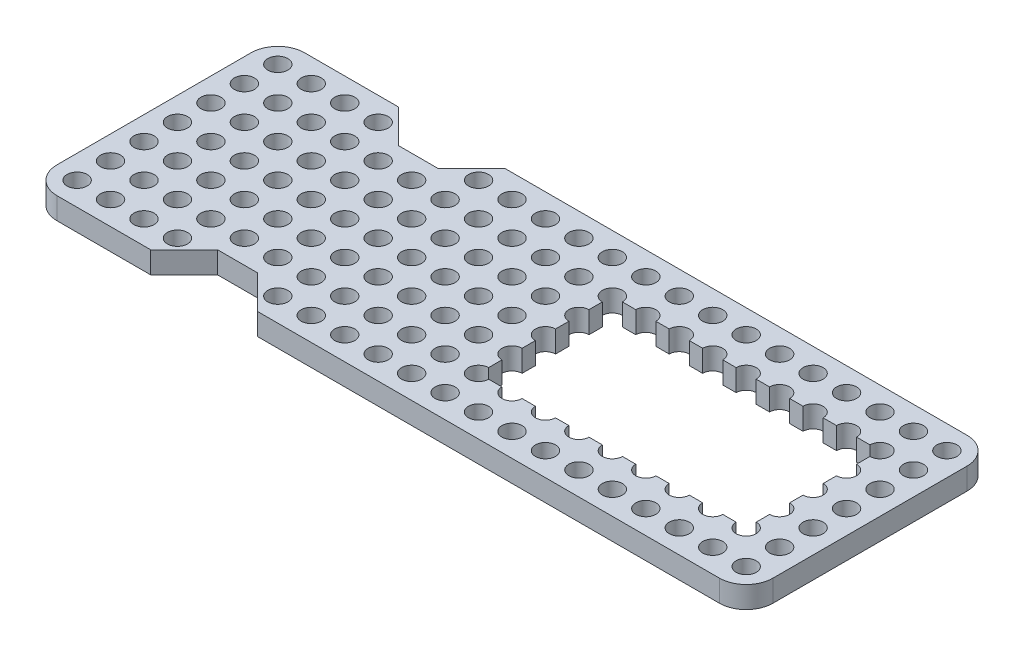
SolidWorks part; units mm, degrees
material "ABS"
ref_plane "Front Plane" through (0, 0, 0) normal (0, 0, 1) x (1, 0, 0)
ref_plane "Top Plane" through (0, 0, 0) normal (0, 1, 0) x (1, 0, 0)
ref_plane "Right Plane" through (0, 0, 0) normal (1, 0, 0) x (0, 0, -1)
sketch "Sketch1" plane through (0, 0, 0) normal (0, 1, 0) x (1, 0, 0)
  line L0 (-35.5, 18.5) -> (-35.5, -18.5) construction
  line L1 (-49.5, 18.5) -> (-35.5, 18.5)
  line L2 (-53.5, 14.5) -> (-53.5, -14.5)
  line L3 (-49.5, -18.5) -> (-35.5, -18.5)
  line L4 (53.5, 14.5) -> (53.5, -14.5)
  line L5 (-53.5, 18.5) -> (53.5, -18.5) construction
  line L6 (-19.5, -18.5) -> (-24.5, -13.5)
  line L7 (-24.5, -13.5) -> (-30.5, -13.5)
  line L8 (-30.5, -13.5) -> (-35.5, -18.5)
  line L9 (-35.5, 18.5) -> (-30.5, 13.5)
  line L10 (-30.5, 13.5) -> (-24.5, 13.5)
  line L11 (-24.5, 13.5) -> (-19.5, 18.5)
  line L12 (-19.5, -18.5) -> (49.5, -18.5)
  line L13 (-19.5, 18.5) -> (49.5, 18.5)
  line L14 (45, -10) -> (45, 10)
  line L15 (45, 10) -> (5, 10)
  line L16 (5, 10) -> (5, -10)
  line L17 (5, -10) -> (45, -10)
  arc A0 (-49.5, 18.5) -> (-53.5, 14.5) centre (-49.5, 14.5) ccw
  arc A1 (-53.5, -14.5) -> (-49.5, -18.5) centre (-49.5, -14.5) ccw
  arc A2 (49.5, -18.5) -> (53.5, -14.5) centre (49.5, -14.5) ccw
  arc A3 (49.5, 18.5) -> (53.5, 14.5) centre (49.5, 14.5) cw
  circle A4 centre (-50, -15) radius 1.5025
  circle A5 centre (-45, -15) radius 1.5025
  circle A6 centre (-40, -15) radius 1.5025
  circle A7 centre (-35, -15) radius 1.5025
  circle A10 centre (-20, -15) radius 1.5025
  circle A11 centre (-15, -15) radius 1.5025
  circle A12 centre (-10, -15) radius 1.5025
  circle A13 centre (-5, -15) radius 1.5025
  circle A14 centre (0, -15) radius 1.5025
  circle A15 centre (5, -15) radius 1.5025
  circle A16 centre (10, -15) radius 1.5025
  circle A17 centre (15, -15) radius 1.5025
  circle A18 centre (20, -15) radius 1.5025
  circle A19 centre (25, -15) radius 1.5025
  circle A20 centre (30, -15) radius 1.5025
  circle A21 centre (35, -15) radius 1.5025
  circle A22 centre (40, -15) radius 1.5025
  circle A23 centre (45, -15) radius 1.5025
  circle A24 centre (50, -15) radius 1.5025
  circle A25 centre (-45, -10) radius 1.5025
  circle A26 centre (-40, -10) radius 1.5025
  circle A27 centre (-35, -10) radius 1.5025
  circle A28 centre (-30, -10) radius 1.5025
  circle A29 centre (-25, -10) radius 1.5025
  circle A30 centre (-20, -10) radius 1.5025
  circle A31 centre (-15, -10) radius 1.5025
  circle A32 centre (-10, -10) radius 1.5025
  circle A33 centre (-5, -10) radius 1.5025
  circle A34 centre (0, -10) radius 1.5025
  arc A35 (5, -8.4975) -> (6.5025, -10) centre (5, -10) ccw
  arc A36 (8.4975, -10) -> (11.5025, -10) centre (10, -10) ccw
  arc A37 (13.4975, -10) -> (16.5025, -10) centre (15, -10) ccw
  arc A38 (18.4975, -10) -> (21.5025, -10) centre (20, -10) ccw
  arc A39 (23.4975, -10) -> (26.5025, -10) centre (25, -10) ccw
  arc A40 (28.4975, -10) -> (31.5025, -10) centre (30, -10) ccw
  arc A41 (33.4975, -10) -> (36.5025, -10) centre (35, -10) ccw
  arc A42 (38.4975, -10) -> (41.5025, -10) centre (40, -10) ccw
  arc A43 (43.4975, -10) -> (45, -8.4975) centre (45, -10) ccw
  circle A44 centre (50, -10) radius 1.5025
  circle A45 centre (-45, -5) radius 1.5025
  circle A46 centre (-40, -5) radius 1.5025
  circle A47 centre (-35, -5) radius 1.5025
  circle A48 centre (-30, -5) radius 1.5025
  circle A49 centre (-25, -5) radius 1.5025
  circle A50 centre (-20, -5) radius 1.5025
  circle A51 centre (-15, -5) radius 1.5025
  circle A52 centre (-10, -5) radius 1.5025
  circle A53 centre (-5, -5) radius 1.5025
  circle A54 centre (0, -5) radius 1.5025
  arc A55 (5, -3.4975) -> (5, -6.5025) centre (5, -5) ccw
  arc A63 (45, -6.5025) -> (45, -3.4975) centre (45, -5) ccw
  circle A64 centre (50, -5) radius 1.5025
  circle A65 centre (-45, 0) radius 1.5025
  circle A66 centre (-40, 0) radius 1.5025
  circle A67 centre (-35, 0) radius 1.5025
  circle A68 centre (-30, 0) radius 1.5025
  circle A69 centre (-25, 0) radius 1.5025
  circle A70 centre (-20, 0) radius 1.5025
  circle A71 centre (-15, 0) radius 1.5025
  circle A72 centre (-10, 0) radius 1.5025
  circle A73 centre (-5, 0) radius 1.5025
  circle A74 centre (0, 0) radius 1.5025
  arc A75 (5, 1.5025) -> (5, -1.5025) centre (5, 0) ccw
  arc A83 (45, -1.5025) -> (45, 1.5025) centre (45, 0) ccw
  circle A84 centre (50, 0) radius 1.5025
  circle A85 centre (-45, 5) radius 1.5025
  circle A86 centre (-40, 5) radius 1.5025
  circle A87 centre (-35, 5) radius 1.5025
  circle A88 centre (-30, 5) radius 1.5025
  circle A89 centre (-25, 5) radius 1.5025
  circle A90 centre (-20, 5) radius 1.5025
  circle A91 centre (-15, 5) radius 1.5025
  circle A92 centre (-10, 5) radius 1.5025
  circle A93 centre (-5, 5) radius 1.5025
  circle A94 centre (0, 5) radius 1.5025
  arc A95 (5, 6.5025) -> (5, 3.4975) centre (5, 5) ccw
  arc A103 (45, 3.4975) -> (45, 6.5025) centre (45, 5) ccw
  circle A104 centre (50, 5) radius 1.5025
  circle A105 centre (-45, 10) radius 1.5025
  circle A106 centre (-40, 10) radius 1.5025
  circle A107 centre (-35, 10) radius 1.5025
  circle A108 centre (-30, 10) radius 1.5025
  circle A109 centre (-25, 10) radius 1.5025
  circle A110 centre (-20, 10) radius 1.5025
  circle A111 centre (-15, 10) radius 1.5025
  circle A112 centre (-10, 10) radius 1.5025
  circle A113 centre (-5, 10) radius 1.5025
  circle A114 centre (0, 10) radius 1.5025
  arc A115 (6.5025, 10) -> (5, 8.4975) centre (5, 10) ccw
  arc A116 (11.5025, 10) -> (8.4975, 10) centre (10, 10) ccw
  arc A117 (16.5025, 10) -> (13.4975, 10) centre (15, 10) ccw
  arc A118 (21.5025, 10) -> (18.4975, 10) centre (20, 10) ccw
  arc A119 (26.5025, 10) -> (23.4975, 10) centre (25, 10) ccw
  arc A120 (31.5025, 10) -> (28.4975, 10) centre (30, 10) ccw
  arc A121 (36.5025, 10) -> (33.4975, 10) centre (35, 10) ccw
  arc A122 (41.5025, 10) -> (38.4975, 10) centre (40, 10) ccw
  arc A123 (45, 8.4975) -> (43.4975, 10) centre (45, 10) ccw
  circle A124 centre (50, 10) radius 1.5025
  circle A125 centre (-45, 15) radius 1.5025
  circle A126 centre (-40, 15) radius 1.5025
  circle A127 centre (-35, 15) radius 1.5025
  circle A130 centre (-20, 15) radius 1.5025
  circle A131 centre (-15, 15) radius 1.5025
  circle A132 centre (-10, 15) radius 1.5025
  circle A133 centre (-5, 15) radius 1.5025
  circle A134 centre (0, 15) radius 1.5025
  circle A135 centre (5, 15) radius 1.5025
  circle A136 centre (10, 15) radius 1.5025
  circle A137 centre (15, 15) radius 1.5025
  circle A138 centre (20, 15) radius 1.5025
  circle A139 centre (25, 15) radius 1.5025
  circle A140 centre (30, 15) radius 1.5025
  circle A141 centre (35, 15) radius 1.5025
  circle A142 centre (40, 15) radius 1.5025
  circle A143 centre (45, 15) radius 1.5025
  circle A144 centre (50, 15) radius 1.5025
  circle A145 centre (-50, -10) radius 1.5025
  circle A146 centre (-50, -5) radius 1.5025
  circle A147 centre (-50, 0) radius 1.5025
  circle A148 centre (-50, 5) radius 1.5025
  circle A149 centre (-50, 10) radius 1.5025
  circle A150 centre (-50, 15) radius 1.5025
  arc A151 (-30.6475, -13.6442) -> (-31.3558, -14.3525) centre (-30, -15) ccw [skipped]
  arc A152 (-24.3525, -13.6442) -> (-25, -13.4975) centre (-25, -15) ccw [skipped]
  arc A153 (-25, 13.4975) -> (-24.3525, 13.6442) centre (-25, 15) ccw [skipped]
  arc A154 (-30.6475, 13.6442) -> (-30, 13.4975) centre (-30, 15) ccw [skipped]
  circle A155 centre (40, -5) radius 1.5025 [skipped]
  circle A156 centre (40, 0) radius 1.5025 [skipped]
  circle A157 centre (40, 5) radius 1.5025 [skipped]
  circle A158 centre (35, 5) radius 1.5025 [skipped]
  circle A159 centre (35, 0) radius 1.5025 [skipped]
  circle A160 centre (35, -5) radius 1.5025 [skipped]
  circle A161 centre (30, -5) radius 1.5025 [skipped]
  circle A162 centre (30, 0) radius 1.5025 [skipped]
  circle A163 centre (30, 5) radius 1.5025 [skipped]
  circle A164 centre (10, 0) radius 1.5025 [skipped]
  circle A165 centre (10, 5) radius 1.5025 [skipped]
  circle A166 centre (15, 5) radius 1.5025 [skipped]
  circle A167 centre (15, 0) radius 1.5025 [skipped]
  circle A168 centre (20, 0) radius 1.5025 [skipped]
  circle A169 centre (20, 5) radius 1.5025 [skipped]
  circle A170 centre (25, 5) radius 1.5025 [skipped]
  circle A171 centre (25, 0) radius 1.5025 [skipped]
  circle A172 centre (25, -5) radius 1.5025 [skipped]
  circle A173 centre (20, -5) radius 1.5025 [skipped]
  arc A174 (16.3524, -5.6546) -> (13.5321, -4.6793) centre (15, -5) ccw [skipped]
  arc A175 (10.8216, -3.7421) -> (10.1309, -3.5032) centre (10, -5) ccw [skipped]
  point P23 (53.5, 18.5)
  dimension "D8" = 4
  dimension "D11" = 3.005
  dimension "D16" = 3.5
  dimension "D1" = 107
  dimension "D2" = 37
  dimension "D3" = 18
  dimension "D4" = 16
  dimension "D5" = 6
  dimension "D6" = 16
  dimension "D7" = 27
  dimension "D9" = 3.5
  dimension "D10" = 3.5
  dimension "D14" = 3.5
  dimension "D15" = 3.5
  dimension "D17" = 3.5
  dimension "D12" = 21
  dimension "D13" = 7
extrude "Boss-Extrude1" add sketch "Sketch1" along normal blind 3.25 contours A3 L13 L11 L10 L9 L1 A0 L2 A1 L3 L8 L7 L6 L12 A2 L4 A150 A149 A148 A147 A146 A145 A144 A143 A142 A141 A140 A139 A138 A137 A136 A135 A134
